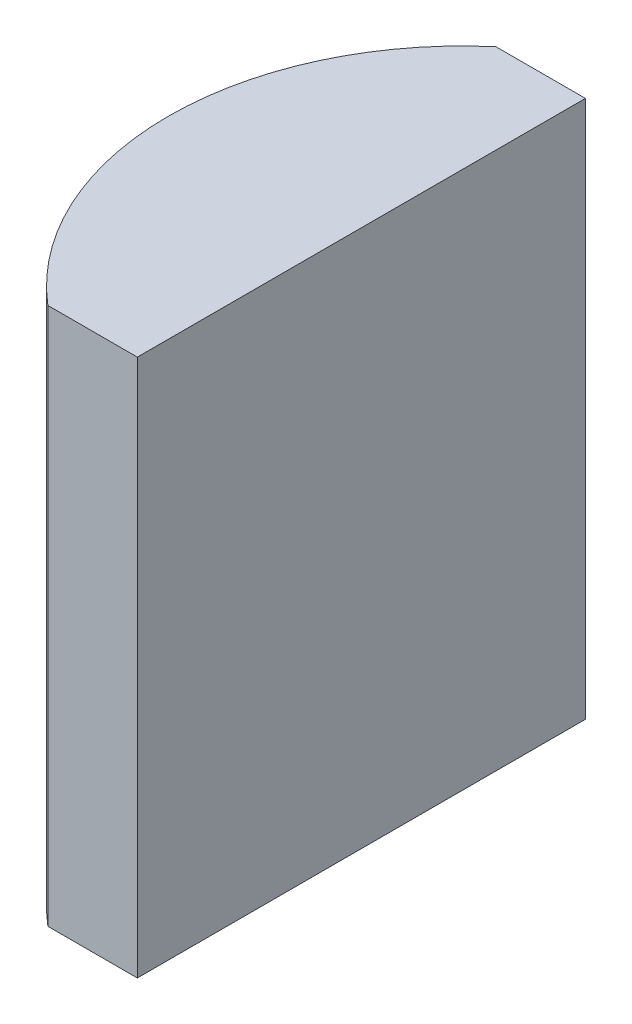
SolidWorks part; units mm, degrees
ref_plane "前视基准面" through (0, 0, 0) normal (0, 0, 1) x (1, 0, 0)
ref_plane "上视基准面" through (0, 0, 0) normal (0, 1, 0) x (1, 0, 0)
ref_plane "右视基准面" through (0, 0, 0) normal (1, 0, 0) x (0, 0, -1)
sketch "草图1" plane through (0, 0, 0) normal (0, 1, 0) x (1, 0, 0)
  line L0 (10.7432, 0) -> (-9.7696, 0) construction
  line L1 (0.1086, 5) -> (2.1052, 5)
  line L2 (0.1086, -5) -> (2.1052, -5)
  line L3 (2.1052, 5) -> (2.1052, -5)
  arc A0 (0.1086, 5) -> (0.1086, -5) centre (4.3552, 0) ccw
  point P19 (-2.2048, 0)
  point P20 (2.1052, 0)
  dimension "D2" = 5
  dimension "D3" = 6.56
  dimension "D4" = 4.31
  dimension "D1" = 5
extrude "凸台-拉伸1" add sketch "草图1" along normal blind 12
